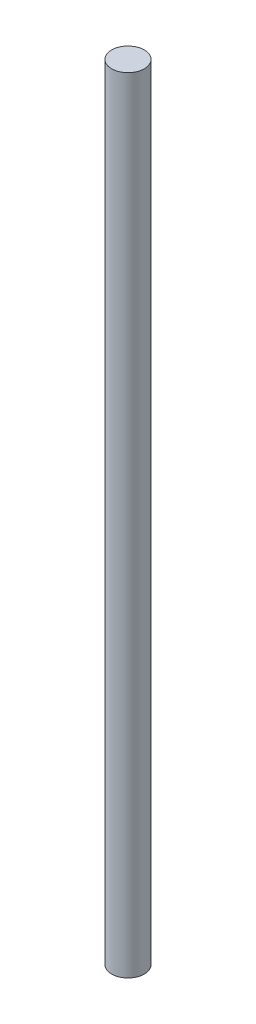
SolidWorks part; units mm, degrees
ref_plane "Front Plane" through (0, 0, 0) normal (0, 0, 1) x (1, 0, 0)
ref_plane "Top Plane" through (0, 0, 0) normal (0, 1, 0) x (1, 0, 0)
ref_plane "Right Plane" through (0, 0, 0) normal (1, 0, 0) x (0, 0, -1)
sketch "Sketch1" plane through (0, 0, 0) normal (0, 1, 0) x (1, 0, 0)
  circle A0 centre (0, 0) radius 2.5
  dimension "D1" = 5
extrude "Boss-Extrude1" add sketch "Sketch1" along normal blind 120
